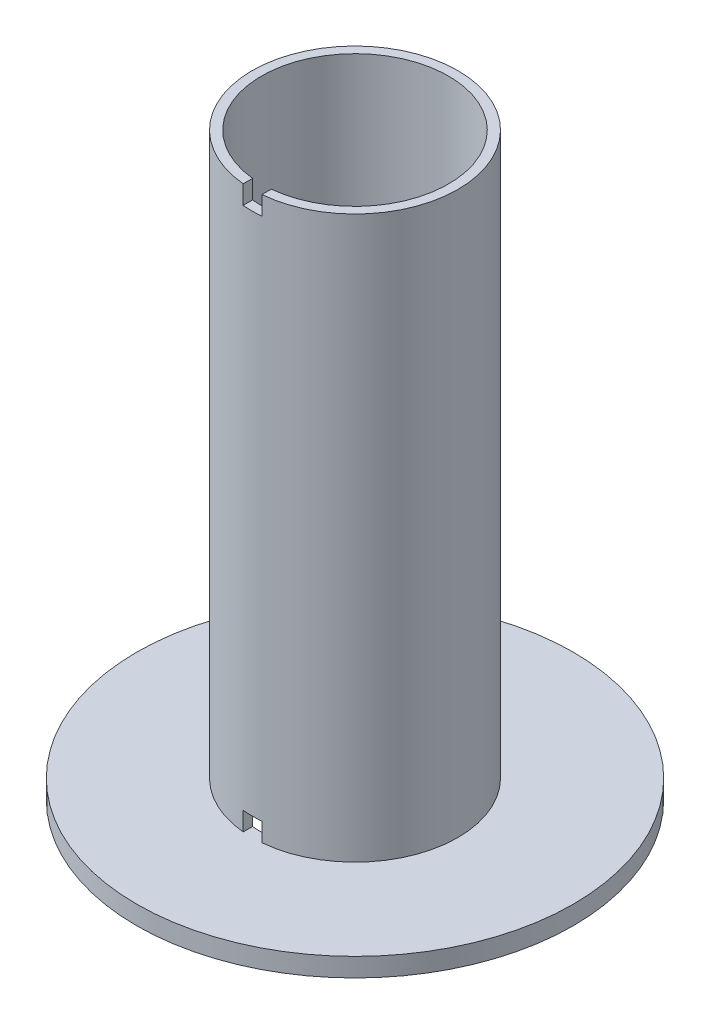
SolidWorks part; units mm, degrees
ref_plane "Front Plane" through (0, 0, 0) normal (0, 0, 1) x (1, 0, 0)
ref_plane "Top Plane" through (0, 0, 0) normal (0, 1, 0) x (1, 0, 0)
ref_plane "Right Plane" through (0, 0, 0) normal (1, 0, 0) x (0, 0, -1)
sketch "Sketch1" plane through (0, 0, 0) normal (0, 1, 0) x (1, 0, 0)
  circle A0 centre (0, 0) radius 38.1
  circle A1 centre (0, 0) radius 88.9
  dimension "D1" = 76.2
  dimension "D2" = 177.8
extrude "Boss-Extrude1" add sketch "Sketch1" along normal blind 7.62
sketch "Sketch2" plane through (0, 7.62, 0) normal (0, 1, 0) x (1, 0, 0)
  circle A0 centre (0, 0) radius 38.1
  circle A1 centre (0, 0) radius 41.91
  dimension "D1" = 3.81
extrude "Boss-Extrude2" add sketch "Sketch2" along normal blind 228.6
sketch "Sketch3" plane through (0, 0, 0) normal (0, 0, 1) x (1, 0, 0)
  line L0 (88.9, 7.62) -> (-88.9, 7.62) construction
  line L1 (-3.81, 15.24) -> (3.81, 15.24)
  line L2 (-3.81, 15.24) -> (-3.81, 7.62)
  line L3 (-3.81, 7.62) -> (3.81, 7.62)
  line L4 (3.81, 15.24) -> (3.81, 7.62)
  line L5 (0, 0) -> (0, 15.24) construction
  line L6 (-41.91, 121.92) -> (41.91, 121.92) construction
  line L7 (-41.91, 236.22) -> (-41.91, 7.62) construction
  line L8 (41.91, 7.62) -> (41.91, 236.22) construction
  line L9 (0, 7.62) -> (0, 236.22) construction
  line L10 (38.1, 236.22) -> (-38.1, 236.22) construction
  line L11 (-3.81, 236.22) -> (3.81, 236.22)
  line L12 (3.81, 228.6) -> (3.81, 236.22)
  line L13 (-3.81, 228.6) -> (-3.81, 236.22)
  line L14 (-3.81, 228.6) -> (3.81, 228.6)
  point P19 (0, 121.92)
  dimension "D1" = 7.62
  dimension "D2" = 7.62
extrude "Cut-Extrude1" cut sketch "Sketch3" along normal through all
